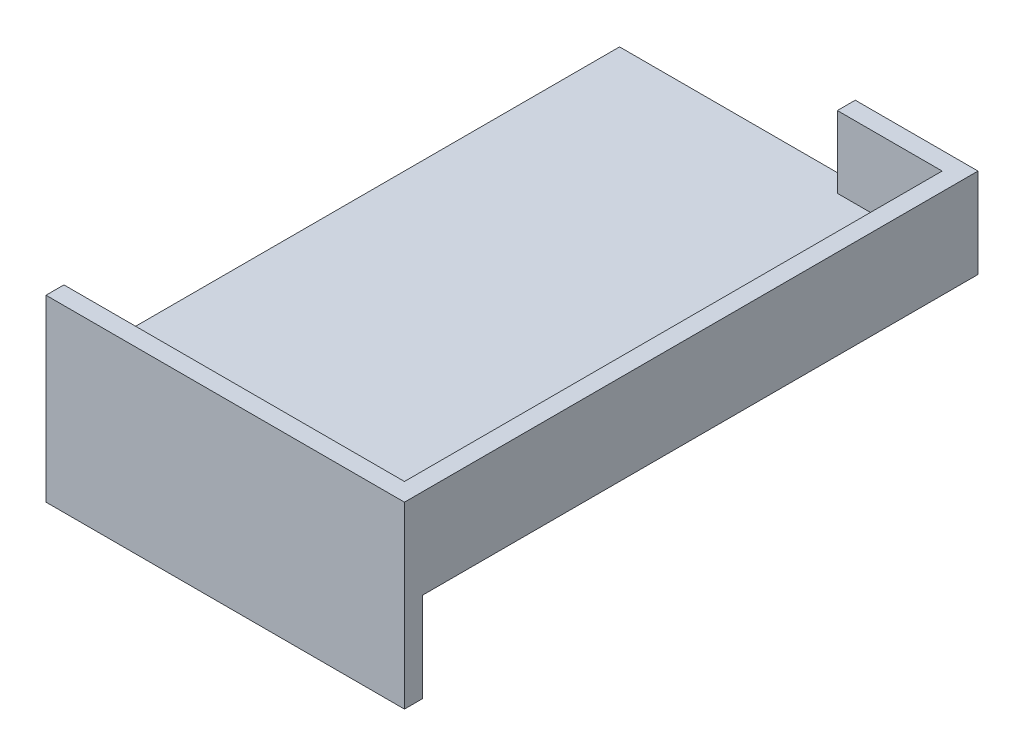
SolidWorks part; units mm, degrees
ref_plane "Front Plane" through (0, 0, 0) normal (0, 0, 1) x (1, 0, 0)
ref_plane "Top Plane" through (0, 0, 0) normal (0, 1, 0) x (1, 0, 0)
ref_plane "Right Plane" through (0, 0, 0) normal (1, 0, 0) x (0, 0, -1)
sketch "Sketch1" plane through (0, 0, 0) normal (0, 1, 0) x (1, 0, 0)
  line L1 (-50, 0) -> (50, 0)
  line L2 (-50, 0) -> (-50, 160)
  line L3 (-50, 160) -> (50, 160)
  line L4 (50, 0) -> (50, 160)
  dimension "D1" = 100
  dimension "D2" = 160
extrude "Boss-Extrude1" add sketch "Sketch1" along normal blind 5
sketch "Sketch2" plane through (0, 0, 0) normal (0, 0, 1) x (1, 0, 0)
  line L1 (50, -25) -> (-50, -25)
  line L2 (50, -25) -> (50, 25)
  line L3 (50, 25) -> (-50, 25)
  line L4 (-50, -25) -> (-50, 25)
  line L5 (-50, -25) -> (50, 25) construction
  line L6 (-50, 25) -> (50, -25) construction
  dimension "D1" = 50
  dimension "D2" = 100
extrude "Boss-Extrude2" add sketch "Sketch2" against normal blind 5
sketch "Sketch4" plane through (50, 0, 0) normal (1, 0, 0) x (0, 0, -1)
  line L0 (160, 5) -> (160, 0) construction
  line L1 (0, 0) -> (160, 0)
  line L2 (0, 0) -> (0, 25)
  line L3 (0, 25) -> (160, 25)
  line L4 (160, 0) -> (160, 25)
  line L5 (5, 25) -> (0, 25) construction
extrude "Boss-Extrude3" add sketch "Sketch4" against normal blind 5
sketch "Sketch5" plane through (0, 0, -160) normal (0, 0, -1) x (-1, 0, 0)
  line L0 (-45, 25) -> (-50, 25) construction
  line L1 (-50, 0) -> (-15.7633, 0)
  line L2 (-50, 0) -> (-50, 25)
  line L3 (-50, 25) -> (-15.7633, 25)
  line L4 (-15.7633, 0) -> (-15.7633, 25)
extrude "Boss-Extrude4" add sketch "Sketch5" against normal blind 5
